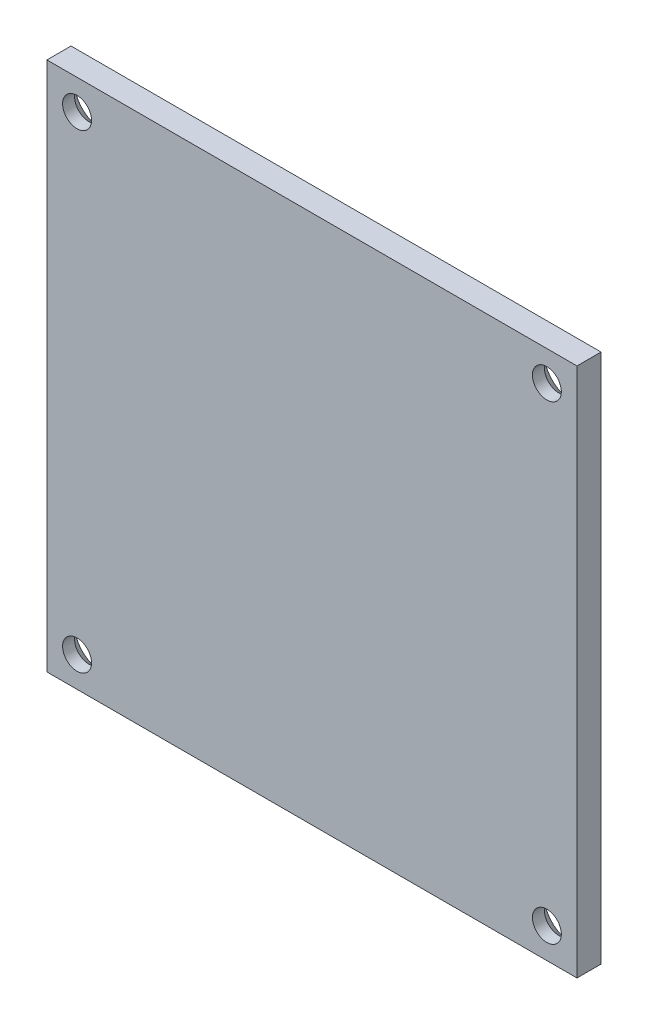
SolidWorks part; units mm, degrees
ref_plane "Plan de face" through (0, 0, 0) normal (1, 0, 0) x (0, 1, 0)
ref_plane "Plan de dessus" through (0, 0, 0) normal (0, 0, 1) x (0, 1, 0)
ref_plane "Plan de droite" through (0, 0, 0) normal (0, 1, 0) x (-1, 0, 0)
sketch "Esquisse1" plane through (0, 0, 0) normal (0, 0, 1) x (0, 1, 0)
  line L1 (-22, -22) -> (22, -22)
  line L2 (-22, -22) -> (-22, 22)
  line L3 (-22, 22) -> (22, 22)
  line L4 (22, -22) -> (22, 22)
  line L5 (-22, -22) -> (22, 22) construction
  line L6 (-22, 22) -> (22, -22) construction
  point P0 (0, 0)
  dimension "D1" = 44
extrude "Boss.-Extru.1" add sketch "Esquisse1" along normal blind 2
hole_wizard "Fraisage pour vis à tête fraisée M21" positions "Esquisse2" profile "Esquisse3" countersink size "M2" standard "Ansi Metric" end condition through all
sketch "Esquisse2" plane through (0, 0, 0) normal (0, 0, -1) x (-1, 0, 0)
  line L0 (-22, 22) -> (22, 22) construction
  line L1 (-22, -22) -> (-22, 22) construction
  line L2 (22, 22) -> (22, -22) construction
  point P0 (-19.5, 19.5)
  point P2 (19.5, 19.5)
  dimension "D2" = 2.5
  dimension "D3" = 2.5
sketch "Esquisse3" plane through (19.5, 19.5, 0) normal (1, 0, 0) x (0, 1, 0)
  line L0 (0, 0) -> (0, 2)
  line L1 (0, 2) -> (1.2, 2)
  line L2 (1.2, 2) -> (1.2, 1)
  line L3 (1.2, 1) -> (2.2, 0)
  line L5 (2.2, 0) -> (0, 0)
  line L6 (-1.2, 1) -> (-2.2, 0) construction
  line L11 (0, -6.35) -> (0, 107.95) construction
  dimension "Diamètre du perçage jusqu'au prochain" = 2.4
  dimension "Profondeur du perçage jusqu'au prochain" = 2
  dimension "Diamètre du fraisage entrant" = 4.4
  dimension "Angle du fraisage entrant" = 90
ref_plane "Plan1" through (0, 0, 0) normal (0, 1, 0) x (1, 0, 0)
mirror "Symétrie2" about plane through (0, 0, 0) normal (0, 1, 0) of "Fraisage pour vis à tête fraisée M21"
equation "\"Plaque_L\"=\"Cavite_L\"+\"Cavite_E\"'longueur plaque"
equation "\"Plaque_H\"= \"Cavite_L\"+\"Cavite_E\"'largeur plaque"
equation "\"Plaque_E\"= 2mm'épaisseur plaque superieure et inferieure"
equation "\"Trou_R\"= 1.2mm'rayon perforation base"
equation "\"Trou_dx\"= 4mm'distance entre trou sur x"
equation "\"Trou-dy\"= 4mm'distance entre trou sur y"
equation "\"Cavite_largeur\"= 28mm'largeur cavité"
equation "\"Cavite_L\"=\"Cavite_largeur\"+\"Cavite_E\"'longueur cavité"
equation "\"Cavite_E\"= 3mm'épaisseur cavité"
equation "\"Cavite_H\"= 18mm'hauteur cavité"
equation "\"Offset_Z\"= 0mm"
equation "\"Vis_Diam\"= 1.6mm"
equation "\"Offset_Bord\"= \"Cavite_E\" / 2"
equation "\"Vis_Long\"= 5mm"
equation "\"Perc_Passage\"= 1.8mm"
equation "\"Perc_Taraud\"= 1.3mm"
equation "\"Fraisure_Diam\"= 3mm"
equation "\"Fraisure_Prof\"= 1mm"
equation "\"Offset_hauteur_vis1\"= \"Cavite_E\""
equation "\"Offset_hauteur_vis2\"= \"Cavite_H\" - \"Cavite_E\""
equation "\"Perc_Profondeur\"= 8mm"
equation "\"Taraud_Profondeur\"= \"Cavite_E\""
equation "\"H_total\"=113mm'122-2*2"
equation "\"espace_trou\"=22.6mm"
equation "\"D1@Esquisse1\"=\"largeur_plaque_enveloppe\""
equation "\"D1@Boss.-Extru.1\"=\"Plaque_E\""
equation "\"D1@Esquisse2\"=\"Offset_Enveloppe\""
equation "\"D2@Esquisse2\"=\"Offset_Enveloppe\""
equation "\"D3@Esquisse2\"=\"Offset_Enveloppe\""
equation "\"Offset_cavite\"= \"Cavite_E\" / 2"
equation "\"espace_vis\"=22.6mm'"
equation "\"Enveloppe_E\"=5mm"
equation "\"Offset_Enveloppe\"= \"Enveloppe_E\" / 2"
equation "\"Largeur_enveloppe\"=\"Cavite_largeur\"+\"Cavite_E\""
equation "\"Longueur_enveloppe\"=\"Cavite_L\"+\"Enveloppe_E\""
equation "\"N_Plaque\"= 7"
equation "\"N_Cavite\"= 6"
equation "\"Largeur_equerre_enveloppe\"=\"Cavite_L\"+\"Cavite_E\""
equation "\"Longueur_enveloppe_enveloppe\"=\"Cavite_L\"+\"Enveloppe_E\""
equation "\"largeur_plaque_enveloppe\"=\"Longueur_equerre_enveloppe\"+\"Enveloppe_E\""
equation "\"Longueur_equerre_enveloppe\"=\"Cavite_L\"+\"Cavite_E\"+\"Enveloppe_E\""
